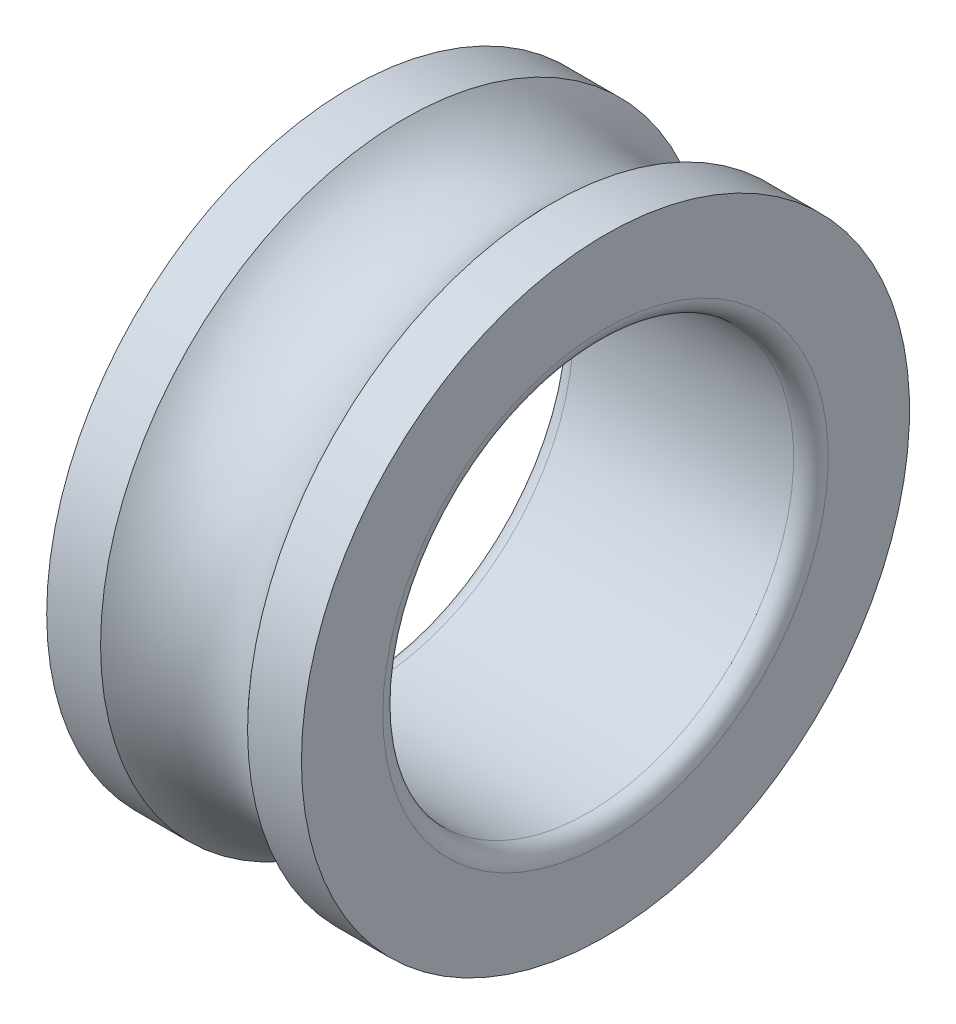
SolidWorks part; units mm, degrees
ref_plane "Płaszczyzna przednia" through (0, 0, 0) normal (0, 0, 1) x (1, 0, 0)
ref_plane "Płaszczyzna górna" through (0, 0, 0) normal (0, 1, 0) x (1, 0, 0)
ref_plane "Płaszczyzna prawa" through (0, 0, 0) normal (1, 0, 0) x (0, 0, -1)
sketch "Sketch1" plane through (0, 0, 0) normal (0, 0, 1) x (1, 0, 0)
  line L0 (0, 0) -> (26.9184, 0) construction
  line L1 (0, 0) -> (0, 33) construction
  line L2 (-15.5, 37) -> (-8.9443, 37)
  line L3 (-15.5, 37) -> (-15.5, 25)
  line L4 (-15.5, 25) -> (15.5, 25)
  line L5 (15.5, 37) -> (15.5, 25)
  line L6 (-15.5, 37) -> (15.5, 25) construction
  line L7 (-15.5, 25) -> (15.5, 37) construction
  line L8 (8.9443, 37) -> (15.5, 37)
  line L9 (0, 37) -> (0, 45.4119) construction
  arc A0 (-8.9443, 37) -> (8.9443, 37) centre (0, 45) ccw
  point P3 (0, 31)
  dimension "D5" = 12
  dimension "D1" = 31
  dimension "D2" = 25
  dimension "D3" = 37
  dimension "D4" = 8
revolve "Revolve1" add sketch "Sketch1" angle 360 about L0
fillet "Fillet1" radius 2.1 2 edges at (-15.5, 0, 25) (15.5, 0, 25)
